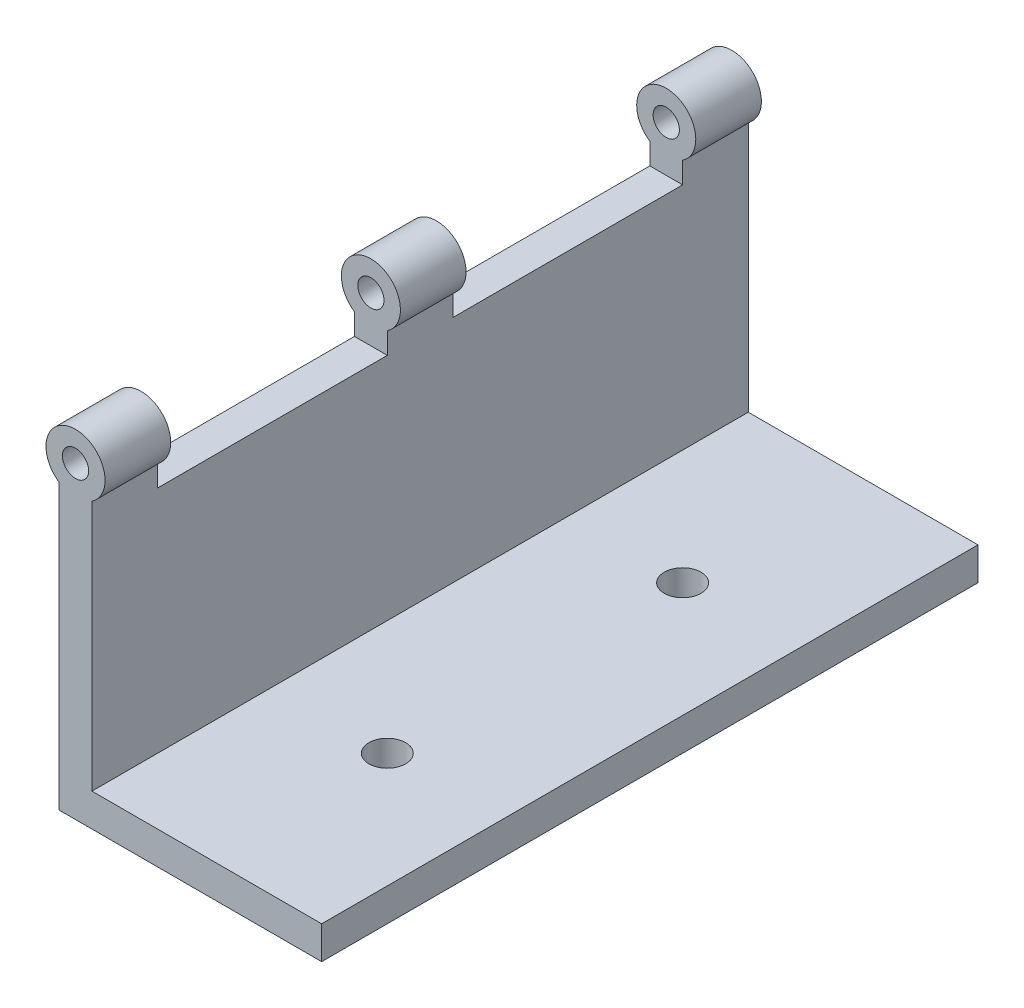
SolidWorks part; units mm, degrees
ref_plane "Front Plane" through (0, 0, 0) normal (0, 0, 1) x (1, 0, 0)
ref_plane "Top Plane" through (0, 0, 0) normal (0, 1, 0) x (1, 0, 0)
ref_plane "Right Plane" through (0, 0, 0) normal (1, 0, 0) x (0, 0, -1)
sketch "Sketch1" plane through (0, 0, 0) normal (0, 0, 1) x (1, 0, 0)
  line L0 (0, 0) -> (0, 40)
  line L1 (0, 0) -> (40, 0)
  line L2 (5, 5) -> (40, 5)
  line L3 (5, 5) -> (5, 40)
  line L4 (0, 40) -> (5, 40)
  line L5 (40, 5) -> (40, 0)
  dimension "D1" = 40
  dimension "D2" = 40
  dimension "D3" = 5
extrude "Boss-Extrude1" add sketch "Sketch1" along normal mid plane 100
sketch "Sketch7" plane through (0, 0, 0) normal (0, 0, 1) x (1, 0, 0)
  line L0 (0, 40) -> (0, 43.2583)
  line L1 (5, 40) -> (5, 43.2583)
  line L2 (0, 43.2583) -> (5, 43.2583)
  line L3 (0, 40) -> (5, 40)
  circle A0 centre (2.5, 47) radius 2
  circle A1 centre (2.5, 47) radius 4.5
  point P13 (2.5, 40)
  dimension "D1" = 4
  dimension "D2" = 9
  dimension "D3" = 7
extrude "Boss-Extrude4" add sketch "Sketch7" along normal mid plane 10 contours A1 L0 L3 L1 | A0
sketch "Sketch2" plane through (0, 0, 50) normal (0, 0, 1) x (1, 0, 0)
  line L0 (5, 40) -> (0, 40) construction
  line L5 (0, 40) -> (0, 43.2583)
  line L6 (5, 40) -> (5, 43.2583)
  line L7 (0, 43.2583) -> (5, 43.2583)
  line L8 (0, 40) -> (5, 40)
  circle A0 centre (2.5, 47) radius 2
  circle A1 centre (2.5, 47) radius 4.5
  point P5 (2.5, 40)
  dimension "D1" = 4
  dimension "D3" = 9
  dimension "D2" = 7
extrude "Boss-Extrude3" add sketch "Sketch2" against normal blind 10 contours A1 | A0 | L8 L6 L7 L5
mirror "Mirror1" about plane through (0, 0, 0) normal (0, 0, 1) of "Boss-Extrude3"
sketch "Sketch12" plane through (0, 5, 0) normal (0, 1, 0) x (1, 0, 0)
  line L0 (22.5, 50) -> (22.5, -50) construction
  line L1 (40, 50) -> (5, 50) construction
  line L2 (40, -50) -> (5, -50) construction
  line L3 (5, 22.5) -> (40, 22.5) construction
  line L4 (5, -50) -> (5, 50) construction
  line L5 (40, -50) -> (40, 50) construction
  line L6 (5, -22.5) -> (40, -22.5) construction
  circle A0 centre (22.5, 22.5) radius 2.8
  circle A1 centre (22.5, -22.5) radius 2.8
  point P18 (0, 0)
  point P19 (0, 0)
  point P20 (0, 0)
  point P21 (0, 0)
  dimension "D4" = 5.6
  dimension "D5" = 5.6
  dimension "D1" = 17.5
  dimension "D2" = 27.5
  dimension "D3" = 27.5
extrude "Cut-Extrude1" cut sketch "Sketch12" against normal through all
